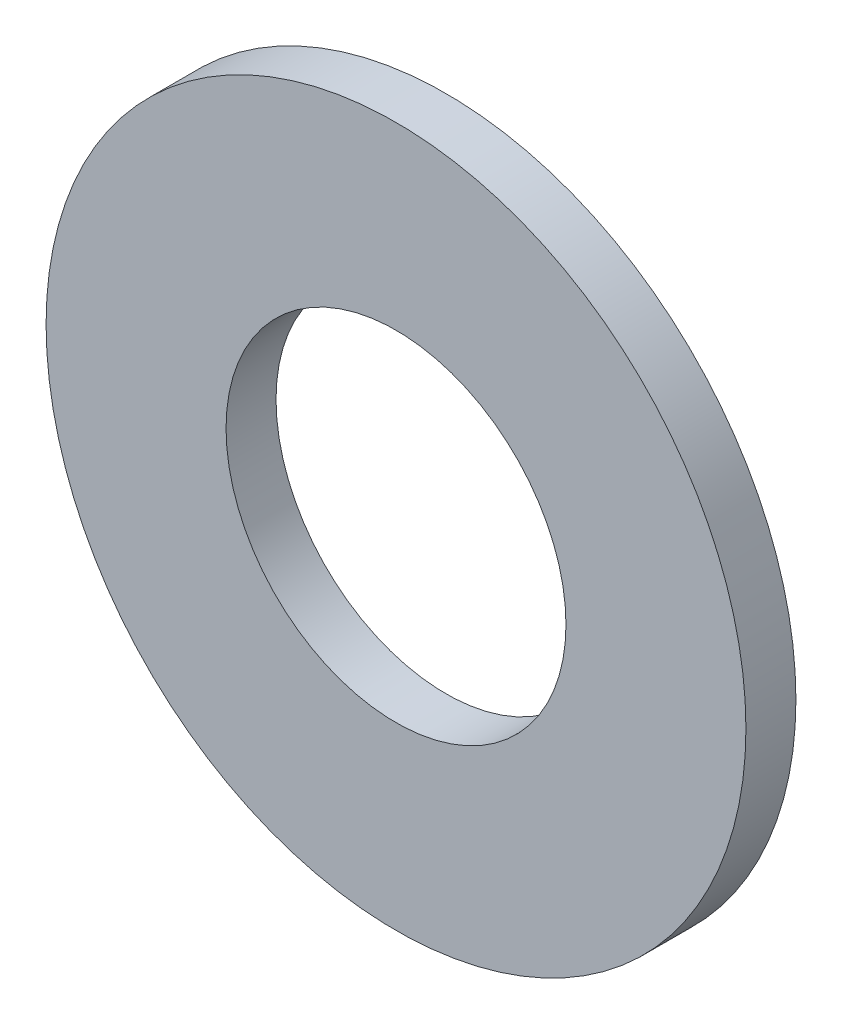
SolidWorks part; units mm, degrees
ref_plane "Front" through (0, 0, 0) normal (0, 0, 1) x (1, 0, 0)
ref_plane "Top" through (0, 0, 0) normal (0, 1, 0) x (1, 0, 0)
ref_plane "Right" through (0, 0, 0) normal (1, 0, 0) x (0, 0, -1)
sketch "Sketch1" plane through (0, 0, 0) normal (0, 0, 1) x (1, 0, 0)
  circle A0 centre (0, 0) radius 1.7
  circle A1 centre (0, 0) radius 3.5
  dimension "d1" = 3.4
  dimension "d2" = 7
extrude "Base-Extrude" add sketch "Sketch1" against normal blind 0.5
